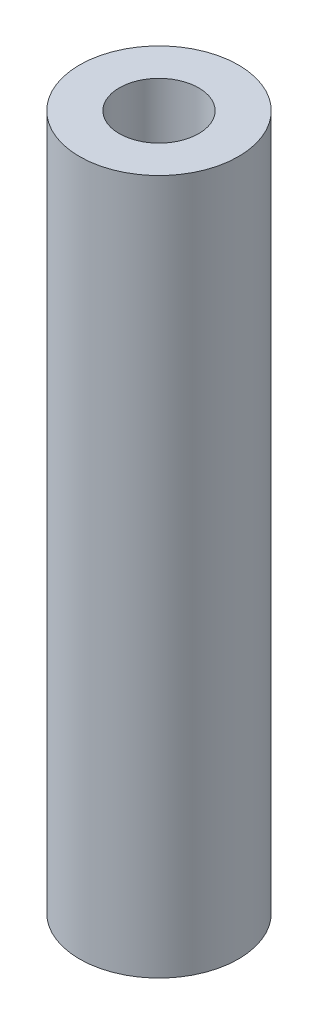
SolidWorks part; units mm, degrees
ref_plane "Alzado" through (0, 0, 0) normal (0, 0, 1) x (1, 0, 0)
ref_plane "Planta" through (0, 0, 0) normal (0, 1, 0) x (1, 0, 0)
ref_plane "Vista lateral" through (0, 0, 0) normal (1, 0, 0) x (0, 0, -1)
sketch "Croquis1" plane through (0, 0, 0) normal (0, 1, 0) x (1, 0, 0)
  circle A0 centre (0, 0) radius 4
  dimension "D1" = 8
extrude "Saliente-Extruir1" add sketch "Croquis1" along normal blind 35
sketch "Croquis2" plane through (0, 35, 0) normal (0, 1, 0) x (1, 0, 0)
  circle A0 centre (0, 0) radius 2
  dimension "D1" = 4
extrude "Cortar-Extruir1" cut sketch "Croquis2" against normal blind 5
